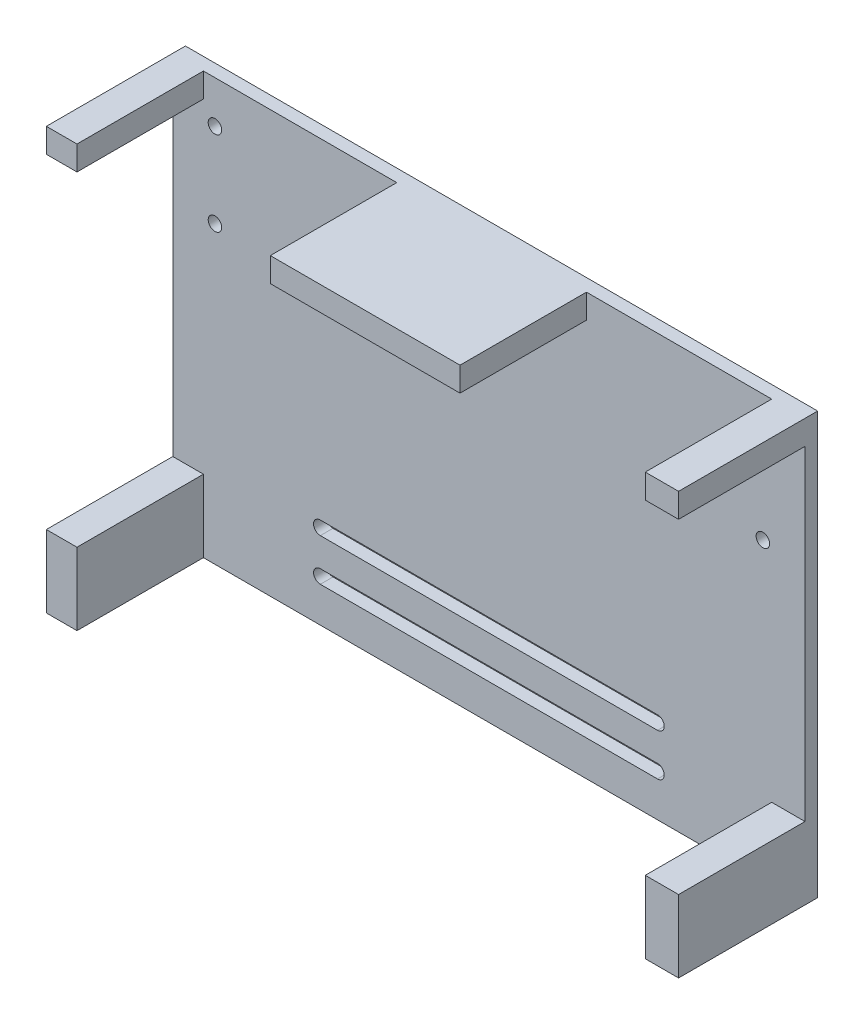
SolidWorks part; units mm, degrees
ref_plane "前视基准面" through (0, 0, 0) normal (0, 0, 1) x (1, 0, 0)
ref_plane "上视基准面" through (0, 0, 0) normal (0, 1, 0) x (1, 0, 0)
ref_plane "右视基准面" through (0, 0, 0) normal (1, 0, 0) x (0, 0, -1)
other "Configuration Table"
sketch "草图1" plane through (0, 0, 0) normal (0, 0, 1) x (1, 0, 0)
  line L0 (-46.7878, 41.3283) -> (-46.7878, 11.3283) construction
  line L1 (-56.7878, 41.3283) -> (93.2122, 41.3283)
  line L2 (-56.7878, 41.3283) -> (-56.7878, -58.6717)
  line L3 (-56.7878, -58.6717) -> (93.2122, -58.6717)
  line L4 (93.2122, 41.3283) -> (93.2122, -58.6717)
  line L5 (-46.7878, 11.3283) -> (-56.7878, 11.3283) construction
  line L6 (-46.7878, 31.3283) -> (-56.7878, 31.3283) construction
  line L7 (18.2122, 41.3283) -> (18.2122, -58.6717) construction
  circle A0 centre (-46.7878, 31.3283) radius 1.6
  circle A1 centre (-46.7878, 11.3283) radius 1.6
  circle A2 centre (83.2122, 11.3283) radius 1.6
  circle A3 centre (83.2122, 31.3283) radius 1.6
  dimension "D5" = 3.2
  dimension "D1" = 150
  dimension "D2" = 100
  dimension "D3" = 10
  dimension "D4" = 30
  dimension "D6" = 20
extrude "凸台-拉伸1" add sketch "草图1" along normal blind 3
sketch "草图2" plane through (0, 0, 3) normal (0, 0, 1) x (1, 0, 0)
  line L0 (93.2122, 41.3283) -> (-56.7878, 41.3283) construction
  line L1 (-3.6519, 41.3283) -> (41.361, 41.3283)
  line L2 (-3.6519, 41.3283) -> (-3.6519, 35.574)
  line L3 (-3.6519, 35.574) -> (41.361, 35.574)
  line L4 (41.361, 41.3283) -> (41.361, 35.574)
  line L5 (93.2122, -58.6717) -> (93.2122, 41.3283) construction
  line L6 (-56.7878, 41.3283) -> (-49.5173, 41.3283)
  line L7 (-56.7878, 41.3283) -> (-56.7878, 35.574)
  line L8 (-56.7878, 35.574) -> (-49.5173, 35.574)
  line L9 (-49.5173, 41.3283) -> (-49.5173, 35.574)
  line L10 (93.2122, 41.3283) -> (85.311, 41.3283)
  line L11 (93.2122, 41.3283) -> (93.2122, 35.574)
  line L12 (93.2122, 35.574) -> (85.311, 35.574)
  line L13 (85.311, 41.3283) -> (85.311, 35.574)
  line L15 (93.2122, -58.6717) -> (85.311, -58.6717)
  line L16 (93.2122, -58.6717) -> (93.2122, -41.5197)
  line L17 (93.2122, -41.5197) -> (85.311, -41.5197)
  line L18 (85.311, -58.6717) -> (85.311, -41.5197)
  line L19 (-56.7878, -58.6717) -> (-49.5173, -58.6717)
  line L20 (-56.7878, -58.6717) -> (-56.7878, -41.5197)
  line L21 (-56.7878, -41.5197) -> (-49.5173, -41.5197)
  line L22 (-49.5173, -58.6717) -> (-49.5173, -41.5197)
extrude "凸台-拉伸2" add sketch "草图2" along normal blind 30
sketch "草图3" plane through (0, 0, 0) normal (0, 0, -1) x (-1, 0, 0)
  line L0 (56.7878, -38.6717) -> (-93.2122, -38.6717) construction
  line L1 (56.7878, 41.3283) -> (56.7878, -58.6717) construction
  line L2 (-93.2122, -58.6717) -> (-93.2122, 41.3283) construction
  line L3 (56.7878, -48.6717) -> (-93.2122, -48.6717) construction
  line L4 (56.7878, -58.6717) -> (-93.2122, -58.6717) construction
  line L5 (-58.2122, -38.6717) -> (21.7878, -38.6717) construction
  line L6 (-58.2122, -37.0717) -> (21.7878, -37.0717)
  line L7 (-58.2122, -40.2717) -> (21.7878, -40.2717)
  line L8 (-58.2122, -48.6717) -> (21.7878, -48.6717) construction
  line L9 (-58.2122, -47.0717) -> (21.7878, -47.0717)
  line L10 (-58.2122, -50.2717) -> (21.7878, -50.2717)
  arc A0 (-58.2122, -37.0717) -> (-58.2122, -40.2717) centre (-58.2122, -38.6717) ccw
  arc A1 (21.7878, -40.2717) -> (21.7878, -37.0717) centre (21.7878, -38.6717) ccw
  arc A2 (-58.2122, -47.0717) -> (-58.2122, -50.2717) centre (-58.2122, -48.6717) ccw
  arc A3 (21.7878, -50.2717) -> (21.7878, -47.0717) centre (21.7878, -48.6717) ccw
  point P12 (-18.2122, -38.6717)
  point P18 (-18.2122, -48.6717)
  dimension "D3" = 1.6
  dimension "D4" = 1.6
  dimension "D1" = 10
  dimension "D2" = 20
  dimension "D5" = 80
  dimension "D6" = 80
extrude "切除-拉伸1" cut sketch "草图3" against normal blind 5
